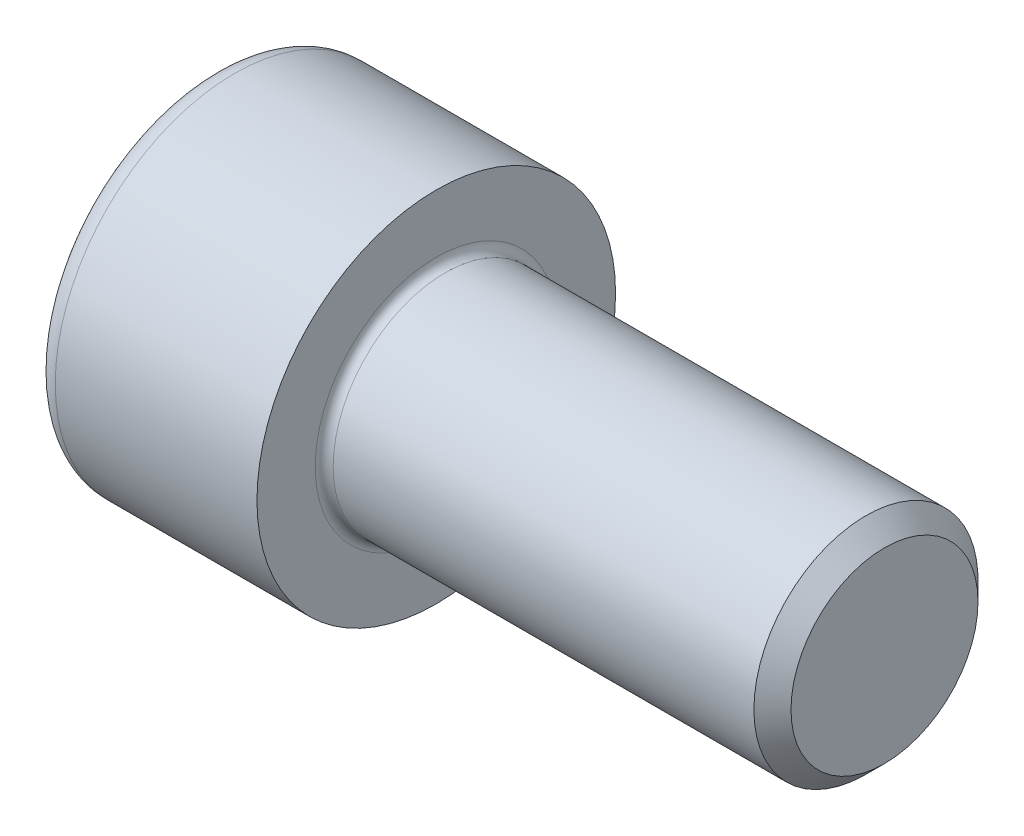
SolidWorks part; units mm, degrees
revolve "Base-Revolve" add sketch "BodySke"
sketch "BodySke" plane through (0, 0, 0) normal (0, 0, 1) x (1, 0, 0)
  line L0 (0, 0) -> (0, 8)
  line L1 (0, 8) -> (10, 8)
  line L2 (10, 8) -> (10, 5)
  line L3 (10, 5) -> (29.172, 5)
  line L4 (30, 4.172) -> (30, 0)
  line L5 (30, 0) -> (0, 0)
  line L6 (-31.75, 0) -> (127, 0) construction
  line L8 (30, 4.172) -> (29.172, 5)
  line L10 (30, -4.172) -> (29.172, -5) construction
  line L11 (11.5, 9.525) -> (11.5, 3.175) construction
  line L12 (10, 9.525) -> (10, 3.175) construction
  line L13 (-30, 9.525) -> (-30, 3.175) construction
  dimension "Head_ht" = 10
  dimension "Length" = 20
  dimension "Body_ch_ang" = 45
  dimension "Diameter" = 10
  dimension "Minor_dia" = 8.344
  dimension "Advance" = 1.5
  dimension "Thread_nom" = 20
  dimension "Thread_length" = 60
  dimension "Head_dia" = 16
cosmetic thread "ThreadCosmetic" [suppressed]
fillet "Fillet1" radius 0.4 1 edges at (10, 0, 5)
fillet "Fillet2" radius 1 1 edges at (0, 0, 8)
ref_plane "Plane1" through (0, 0, 0) normal (0, 0, 1) x (1, 0, 0)
ref_plane "Plane2" through (0, 0, 0) normal (0, 1, 0) x (1, 0, 0)
ref_plane "Plane3" through (0, 0, 0) normal (1, 0, 0) x (0, 0, -1)
sketch "Sketch2" plane through (0, 0, 0) normal (0, 0, 1) x (1, 0, 0)
  line L0 (0, 4.0125) -> (5, 4.0125)
  line L1 (5, 4.0125) -> (7.3166, 0)
  line L2 (-31.75, 0) -> (127, 0) construction
  line L3 (7.3166, 0) -> (0, 0)
  line L4 (0, 0) -> (0, 4.0125)
  line L6 (0, 0) -> (47.625, 0) construction
  dimension "D1" = 4.0125
  dimension "D2" = 60
  dimension "Depth" = 5
revolve "Hex-PreBroach" cut sketch "Sketch2" angle 360 about L6
sketch "Sketch3" plane through (0, 0, 0) normal (-1, 0, 0) x (0, 0.5, 0.866)
  line L0 (2.3166, 4.0125) -> (-2.3166, 4.0125)
  line L1 (-2.3166, 4.0125) -> (-4.6332, 0)
  line L2 (2.3166, 4.0125) -> (4.6332, 0)
  line L3 (2.3166, -4.0125) -> (4.6332, 0)
  line L4 (2.3166, -4.0125) -> (-2.3166, -4.0125)
  line L5 (-2.3166, -4.0125) -> (-4.6332, 0)
  dimension "D1" = 4.0125
  dimension "D2" = 4.0125
  dimension "Hex_size" = 8.025
extrude "Hex" cut sketch "Sketch3" against normal blind 5
sketch "ThdSchSke" plane through (0, 0, 0) normal (0, 0, 1) x (1, 0, 0)
  line L0 (14.5, -4.172) -> (13.9202, -5)
  line L1 (14.5, -4.172) -> (15.0798, -5)
  line L2 (15.0798, -5) -> (15.0798, -6.25)
  line L3 (-3.175, 0) -> (5.1513, 0) construction
  line L4 (0, 7) -> (0, -7) construction
  line L5 (15.0798, -6.25) -> (13.9202, -6.25)
  line L6 (13.9202, -6.25) -> (13.9202, -5)
  dimension "Thread_minor" = 8.344
  dimension "Diameter" = 10
  dimension "Start" = 14.5
revolve "ThreadSchematic" [suppressed] cut sketch "ThdSchSke" angle 360 about L3
pattern_linear "ThdSchPat" [suppressed]
equation "\"D2@Sketch3\" = \"Hex_size@Sketch3\" / 2"
equation "\"D1@Sketch3\" = \"Hex_size@Sketch3\" / 2"
equation "\"D1@Sketch2\" = \"Hex_size@Sketch3\" / 2"
equation "\"Thread_minor@ThreadCosmetic\"  =  \"Minor_dia@BodySke\""
equation "\"Depth@Sketch2\" =  \"Key_eng@Hex\""
equation "\"Thread_length@ThreadCosmetic\" = ((sgn( (\"Length@BodySke\" - \"Advance@BodySke\" * 3.0) - \"Thread_nom@BodySke\" )-1)*( (\"Length@BodySke\" - \"Advance@BodySke\" * 3.0) - \"Thread_nom@BodySke\" ))/-2+ \"Thread_nom@BodySke\""
equation "\"Thread_minor@ThdSchSke\" = \"Minor_dia@BodySke\""
equation "\"Diameter@ThdSchSke\" = \"Diameter@BodySke\""
equation "\"Overcut@ThdSchSke\" = \"Diameter@BodySke\" * 1.25"
equation "\"Start@ThdSchSke\" = \"Head_ht@BodySke\" + \"Length@BodySke\" - \"Thread_length@ThreadCosmetic\"  '---Non-countersunk---"
equation "\"Num_threads@ThdSchPat\" = int( \"Thread_length@ThreadCosmetic\" / \"Advance@BodySke\" + 0.999 )  + 1"
equation "\"Advance@ThdSchPat\" = \"Thread_length@ThreadCosmetic\" /  (\"Num_threads@ThdSchPat\" - 1) 'relax it"
equation "\"Num_threads@ThdSchPat\" = \"Num_threads@ThdSchPat\" - sgn( \"Num_threads@ThdSchPat\" - 1) '---chamfered tips only---"
